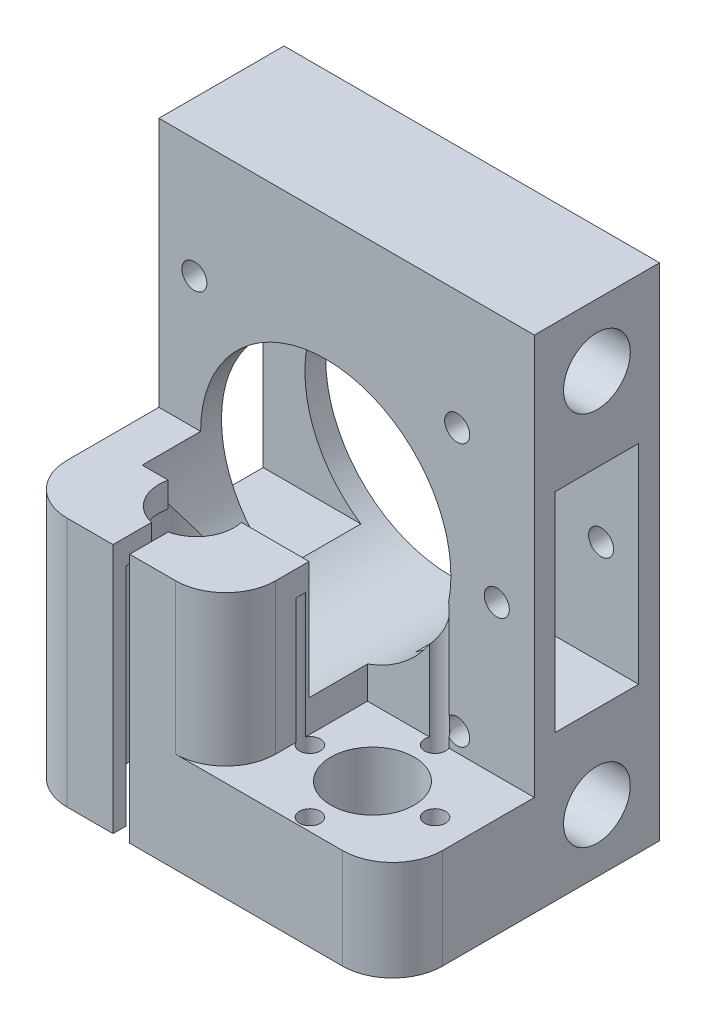
SolidWorks part; units mm, degrees
ref_plane "Front Plane" through (0, 0, 0) normal (0, 0, 1) x (1, 0, 0)
ref_plane "Top Plane" through (0, 0, 0) normal (0, 1, 0) x (1, 0, 0)
ref_plane "Right Plane" through (0, 0, 0) normal (1, 0, 0) x (0, 0, -1)
sketch "Sketch1" plane through (0, 0, 0) normal (0, 0, 1) x (1, 0, 0)
  line L1 (-22.5, -30) -> (22.5, -30)
  line L2 (-22.5, -30) -> (-22.5, 30)
  line L3 (-22.5, 30) -> (22.5, 30)
  line L4 (22.5, -30) -> (22.5, 30)
  line L5 (-22.5, -30) -> (22.5, 30) construction
  line L6 (-22.5, 30) -> (22.5, -30) construction
  point P0 (0, 0)
  dimension "D1" = 45
  dimension "D2" = 60
extrude "Boss-Extrude1" add sketch "Sketch1" along normal blind 15
sketch "Sketch2" plane through (22.5, 0, 0) normal (1, 0, 0) x (0, 0, -1)
  line L0 (-7.5, 30) -> (-7.5, -30) construction
  line L1 (-15, 30) -> (0, 30) construction
  line L2 (-15, -30) -> (0, -30) construction
  line L3 (0, -30) -> (0, 30) construction
  line L4 (-12.5, -12.5) -> (-2.5, -12.5)
  line L5 (-12.5, -12.5) -> (-12.5, 12.5)
  line L6 (-12.5, 12.5) -> (-2.5, 12.5)
  line L7 (-2.5, -12.5) -> (-2.5, 12.5)
  line L8 (-12.5, -12.5) -> (-2.5, 12.5) construction
  line L9 (-12.5, 12.5) -> (-2.5, -12.5) construction
  line L10 (-15, 0) -> (0, 0) construction
  line L11 (-15, -30) -> (-15, 30) construction
  circle A0 centre (-7.5, 22.5) radius 4
  circle A1 centre (-7.5, -22.5) radius 4
  point P6 (-7.5, 0)
  dimension "D3" = 8
  dimension "D1" = 2.5
  dimension "D2" = 25
  dimension "D4" = 22.5
extrude "Cut-Extrude1" cut sketch "Sketch2" against normal through all
sketch "Sketch3" plane through (-22.5, 0, 0) normal (-1, 0, 0) x (0, 0, 1)
  line L1 (15, -30) -> (32, -30)
  line L2 (15, -30) -> (15, -18)
  line L3 (15, -18) -> (32, -18)
  line L4 (32, -30) -> (32, -18)
  dimension "D1" = 17
  dimension "D2" = 12
extrude "Boss-Extrude2" add sketch "Sketch3" against normal up to surface (45 mm away) up to face at (22.5, -22.5, 11.5)
sketch "Sketch4" plane through (0, -18, 0) normal (0, 1, 0) x (1, 0, 0)
  line L1 (-22.5, -32) -> (2.5, -32)
  line L2 (2.5, -15) -> (-22.5, -15)
  line L7 (-22.5, -15) -> (-22.5, -32)
  line L9 (2.5, -15) -> (2.5, -32)
  dimension "D1" = 17
  dimension "D2" = 25
extrude "Boss-Extrude3" add sketch "Sketch4" along normal blind 18
sketch "Sketch5" plane through (0, 0, 32) normal (0, 0, 1) x (1, 0, 0)
  line L0 (-10, 0) -> (-10, -30) construction
  line L1 (2.5, 0) -> (-22.5, 0) construction
  line L2 (22.5, -30) -> (-22.5, -30) construction
  line L4 (-11, -30) -> (-9, -30)
  line L5 (-11, -30) -> (-11, 0)
  line L6 (-11, 0) -> (-9, 0)
  line L7 (-9, -30) -> (-9, 0)
  line L8 (-11, -30) -> (-9, 0) construction
  line L9 (-11, 0) -> (-9, -30) construction
  point P6 (-10, -15)
  dimension "D1" = 2
  dimension "D2" = 30
extrude "Cut-Extrude2" cut sketch "Sketch5" against normal blind 5
sketch "Sketch6" plane through (0, -30, 0) normal (0, -1, 0) x (1, 0, 0)
  line L0 (-10, 27) -> (-10, 15) construction
  line L1 (-9, 27) -> (-11, 27) construction
  line L2 (2.5, 15) -> (-22.5, 15) construction
  circle A0 centre (-10, 23) radius 4.5
  dimension "D1" = 9
  dimension "D2" = 4
extrude "Cut-Extrude3" cut sketch "Sketch6" against normal through all
sketch "Sketch7" plane through (0, -30, 0) normal (0, -1, 0) x (1, 0, 0)
  line L0 (-10, 23) -> (-22.5, 23) construction
  line L1 (-22.5, 32) -> (-22.5, 0) construction
  line L2 (11.1, 23) -> (14.6355, 26.5355) construction
  line L3 (11.1, 23) -> (11.1, 30.5) construction
  line L4 (11.1, 23) -> (14.6355, 19.4645) construction
  circle A0 centre (-10, 23) radius 7.5
  circle A1 centre (11.1, 23) radius 5
  circle A2 centre (18.6, 23) radius 1.25
  circle A3 centre (11.1, 30.5) radius 1.25
  circle A4 centre (11.1, 15.5) radius 1.25
  circle A5 centre (3.6, 23) radius 1.25
  dimension "D1" = 15
  dimension "D2" = 10
  dimension "D4" = 2.5
  dimension "D8" = 2.5
  dimension "D3" = 21.1
  dimension "D5" = 7.5
  dimension "D6" = 45
  dimension "D7" = 7.5
  dimension "D9" = 45
extrude "Cut-Extrude4" cut sketch "Sketch7" against normal offset from surface (27 mm away) 3 up to face at (-10, 0, 25.4859)
sketch "Sketch8" plane through (0, 0, 0) normal (0, 0, -1) x (-1, 0, 0)
  line L0 (2.5, -30) -> (2.5, 30) construction
  line L3 (-22.5, 0) -> (22.5, 0) construction
  line L4 (-22.5, -30) -> (-22.5, 30) construction
  line L5 (22.5, 30) -> (22.5, -30) construction
  line L6 (2.5, 0) -> (18.25, 15.75) construction
  line L7 (22.5, -30) -> (-22.5, -30) construction
  line L8 (-22.5, 30) -> (22.5, 30) construction
  line L9 (-13.25, -15.75) -> (2.5, 0) construction
  line L10 (18.25, -15.75) -> (2.5, 0) construction
  line L11 (2.5, 0) -> (-13.25, 15.75) construction
  circle A0 centre (2.5, 0) radius 15
  circle A1 centre (18.25, 15.75) radius 1.5
  circle A2 centre (-13.25, 15.75) radius 1.5
  circle A3 centre (-13.25, -15.75) radius 1.5
  circle A4 centre (18.25, -15.75) radius 1.5
  dimension "D1" = 30
  dimension "D2" = 3
  dimension "D10" = 3
  dimension "D3" = 0
  dimension "D4" = 45
  dimension "D5" = 31.5
  dimension "D6" = 31.5
  dimension "D7" = 20
  dimension "D8" = 45
  dimension "D9" = 45
extrude "Cut-Extrude5" cut sketch "Sketch8" against normal blind 22
fillet "Fillet1" radius 6 3 edges at (-22.5, -15, 32) (22.5, -24, 32) (2.5, -9, 32)
sketch "Sketch9" plane through (0, 0, 0) normal (0, 0, -1) x (-1, 0, 0)
  line L0 (-22.5, 0) -> (-12.5, 0) construction
  line L1 (-22.5, -30) -> (-22.5, 30) construction
  circle A0 centre (2.5, 0) radius 15 construction
  circle A1 centre (-18, 0) radius 1.5
  dimension "D1" = 3
  dimension "D2" = 4.5
extrude "Cut-Extrude6" cut sketch "Sketch9" against normal up to surface (15 mm away) up to face at (11.75, 15.75, 15)
